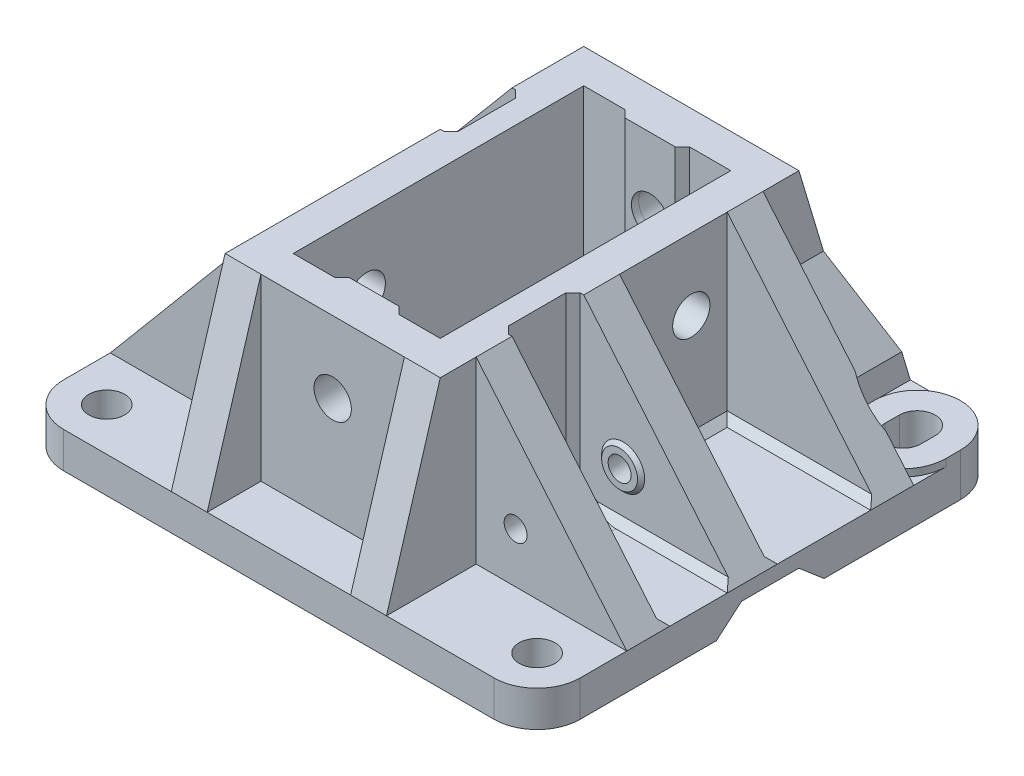
SolidWorks part; units mm, degrees
ref_plane "Front Plane" through (0, 0, 0) normal (0, 0, 1) x (1, 0, 0)
ref_plane "Top Plane" through (0, 0, 0) normal (0, 1, 0) x (1, 0, 0)
ref_plane "Right Plane" through (0, 0, 0) normal (1, 0, 0) x (0, 0, -1)
sketch "Sketch1" plane through (0, 0, 0) normal (0, 1, 0) x (1, 0, 0)
  line L0 (0, 0) -> (0, 65)
  line L1 (0, 0) -> (72, 0)
  line L2 (0, 65) -> (72, 65)
  line L3 (72, 0) -> (72, 65)
  dimension "D1" = 72
  dimension "D2" = 65
extrude "Boss-Extrude1" add sketch "Sketch1" along normal blind 5
sketch "Sketch2" plane through (0, 5, 0) normal (0, 1, 0) x (1, 0, 0)
  line L0 (21, 57.5) -> (21, 7.5)
  line L1 (21, 57.5) -> (51, 57.5)
  line L2 (21, 7.5) -> (51, 7.5)
  line L3 (51, 57.5) -> (51, 7.5)
  line L4 (0, 0) -> (72, 0) construction
  line L7 (72, 0) -> (72, 65) construction
  dimension "D1" = 50
  dimension "D2" = 7.5
  dimension "D3" = 30
  dimension "D4" = 21
extrude "Boss-Extrude2" add sketch "Sketch2" along normal blind 25
sketch "Sketch4" plane through (0, 30, 0) normal (0, 1, 0) x (1, 0, 0)
  line L0 (25.75, 52.75) -> (25.75, 12.25)
  line L1 (25.75, 52.75) -> (46.25, 52.75)
  line L2 (25.75, 12.25) -> (46.25, 12.25)
  line L3 (46.25, 52.75) -> (46.25, 12.25)
  line L4 (51, 57.5) -> (21, 57.5) construction
  line L6 (21, 57.5) -> (21, 7.5) construction
  dimension "D1" = 40.5
  dimension "D2" = 4.75
  dimension "D3" = 20.5
  dimension "D4" = 4.75
extrude "Cut-Extrude1" cut sketch "Sketch4" against normal blind 25
sketch "Sketch5" plane through (51, 0, 0) normal (1, 0, 0) x (0, 0, -1)
  line L0 (57.5, 30) -> (65, 5)
  line L1 (57.5, 5) -> (65, 5)
  line L2 (57.5, 5) -> (57.5, 30)
extrude "Boss-Extrude3" add sketch "Sketch5" against normal blind 5
ref_plane "Plane1" through (36, 0, 0) normal (1, 0, 0) x (0, 0, -1)
mirror "Mirror1" about plane through (36, 0, 0) normal (1, 0, 0) of "Boss-Extrude3"
ref_plane "Plane2" through (0, 0, -32.5) normal (0, 0, 1) x (1, 0, 0)
mirror "Mirror2" about plane through (0, 0, -32.5) normal (0, 0, 1) of "Mirror1", "Boss-Extrude3"
sketch "Sketch6" plane through (0, 0, -7.5) normal (0, 0, 1) x (1, 0, 0)
  line L0 (51, 30) -> (72, 5)
  line L1 (72, 5) -> (51, 5)
  line L2 (51, 5) -> (51, 30)
extrude "Boss-Extrude4" add sketch "Sketch6" against normal blind 5 from offset 5 offset against normal yes
mirror "Mirror3" about plane through (0, 0, -32.5) normal (0, 0, 1) of "Boss-Extrude4"
sketch "Sketch7" plane through (0, 0, -32.5) normal (0, 0, 1) x (1, 0, 0)
  line L0 (51, 30) -> (72, 5)
  line L1 (72, 5) -> (51, 5)
  line L2 (51, 5) -> (51, 30)
extrude "Boss-Extrude5" add sketch "Sketch7" along normal blind 5
mirror "Mirror4" about plane through (36, 0, 0) normal (1, 0, 0) of "Boss-Extrude4", "Mirror3"
sketch "Sketch8" plane through (0, 0, -32.5) normal (0, 0, 1) x (1, 0, 0)
  line L0 (21, 30) -> (0, 5)
  line L1 (0, 5) -> (21, 5)
  line L2 (21, 5) -> (21, 30)
extrude "Boss-Extrude6" add sketch "Sketch8" against normal blind 5
fillet "Fillet1" radius 6 4 edges at (0, 2.5, -65) (0, 2.5, 0) (72, 2.5, 0) (72, 2.5, -65)
sketch "Sketch9" plane through (0, 5, 0) normal (0, 1, 0) x (1, 0, 0)
  line L0 (63.5, 59) -> (63.5, 57)
  line L1 (68.5, 57) -> (68.5, 59)
  line L2 (60, 59) -> (60, 57)
  line L3 (72, 59) -> (72, 57)
  arc A1 (72, 59) -> (60, 59) centre (66, 59) ccw
  arc A2 (63.5, 57) -> (68.5, 57) centre (66, 57) ccw
  arc A3 (68.5, 59) -> (63.5, 59) centre (66, 59) ccw
  arc A4 (72, 59) -> (66, 65) centre (66, 59) ccw construction
  arc A6 (60, 57) -> (72, 57) centre (66, 57) ccw
  point P1 (68.5, 58)
  point P3 (72, 58)
  point P4 (66, 61.5)
  dimension "D1" = 12
  dimension "D2" = 12
  dimension "D3" = 5
  dimension "D4" = 5
  dimension "D5" = 2
  dimension "D6" = 2
  dimension "D7" = 2
  dimension "D8" = 3.5
  dimension "D9" = 3.5
sketch "Sketch10" plane through (72, 0, 0) normal (1, 0, 0) x (0, 0, -1)
  line L0 (36.5, 3) -> (32.5, 3)
  line L1 (0, 0) -> (65, 0) construction
  line L2 (32.5, 5) -> (47.5, 5) construction
  line L3 (36.5, 3) -> (40, 0)
  line L5 (32.5, 5) -> (32.5, 30) construction
  line L6 (28.5, 3) -> (25, 0)
  line L7 (28.5, 3) -> (32.5, 3)
  line L8 (25, 0) -> (40, 0)
  line M7 (6, 0) -> (59, 0)
  dimension "D1" = 4
  dimension "D2" = 25
  dimension "D3" = 3.5
  dimension "D4" = 2
extrude "Cut-Extrude3" cut sketch "Sketch10" against normal blind 75 contours L7 L6 L3 L0 M7
sketch "Sketch11" plane through (0, 5, 0) normal (0, 1, 0) x (1, 0, 0)
  line L0 (51, 0) -> (66, 0) construction
  line L1 (72, 0) -> (72, 65) construction
  circle A0 centre (66, 6) radius 2.5
  dimension "D1" = 5
  dimension "D2" = 6
  dimension "D3" = 6
extrude "Cut-Extrude4" cut sketch "Sketch11" against normal blind 5
mirror "Mirror6" about plane through (36, 0, 0) normal (1, 0, 0) of "Cut-Extrude4"
sketch "Sketch12" plane through (0, 0, -12.5) normal (0, 0, 1) x (1, 0, 0)
  line L0 (51, 30) -> (51, 5) construction
  line L1 (51, 5) -> (72, 5) construction
  circle A0 centre (56.5, 12) radius 1.6
  dimension "D1" = 3.2
  dimension "D2" = 5.5
  dimension "D3" = 7
extrude "Cut-Extrude5" cut sketch "Sketch12" against normal blind 5
sketch "Sketch13" plane through (0, 0, -7.5) normal (0, 0, 1) x (1, 0, 0)
  line L0 (26, 30) -> (46, 30) construction
  line L1 (46, 5) -> (46, 30) construction
  circle A0 centre (36, 20) radius 2.6021
  dimension "D1" = 5.2043
  dimension "D2" = 10
  dimension "D3" = 10
extrude "Cut-Extrude6" cut sketch "Sketch13" against normal blind 7
sketch "Sketch14" plane through (0, 0, -12.25) normal (0, 0, -1) x (-1, 0, 0)
  line L0 (-32.5, 30) -> (-32.5, 5)
  line L1 (-32.5, 30) -> (-39.5, 30)
  line L2 (-32.5, 5) -> (-39.5, 5)
  line L3 (-39.5, 30) -> (-39.5, 5)
  line L4 (-25.75, 30) -> (-46.25, 30) construction
  line L5 (-25.75, 5) -> (-46.25, 5) construction
  dimension "D1" = 7
  dimension "D2" = 6.75
extrude "Boss-Extrude7" add sketch "Sketch14" along normal blind 1
sketch "Sketch15" plane through (0, 30, 0) normal (0, 1, 0) x (1, 0, 0)
  line L0 (39.5, 13.25) -> (40.5, 12.25)
  line L1 (39.5, 12.25) -> (46.25, 12.25) construction
  line L2 (40.5, 12.25) -> (39.5, 12.25)
  line L3 (39.5, 12.25) -> (39.5, 13.25)
  dimension "D1" = 1
extrude "Boss-Extrude8" add sketch "Sketch15" against normal blind 25
mirror "Mirror7" about plane through (36, 0, 0) normal (1, 0, 0) of "Boss-Extrude8"
mirror "Mirror8" about plane through (0, 0, -32.5) normal (0, 0, 1) of "Cut-Extrude6", "Boss-Extrude7", "Mirror7", "Boss-Extrude8"
sketch "Sketch16" plane through (0, 0, -12.25) normal (0, 0, 1) x (1, 0, 0)
  circle A0 centre (36, 20) radius 2.6
  dimension "D1" = 5.2
extrude "Cut-Extrude7" cut sketch "Sketch16" against normal blind 65
ref_plane "Plane3" through (72, 5, -52.5) normal (0, 0, -1) x (-1, 0, 0)
sketch "Sketch21" plane through (0, 30, 0) normal (0, 1, 0) x (1, 0, 0)
  line L0 (21.5, 47.5) -> (22.5, 46.5)
  line L1 (22.5, 46.5) -> (22.5, 38.5)
  line L2 (21, 47.5) -> (21.5, 47.5)
  line L3 (21, 47.5) -> (21, 37.5) construction
  line L4 (21, 47.5) -> (21, 37.5)
  line L5 (21.5, 37.5) -> (22.5, 38.5)
  line L6 (21, 37.5) -> (21.5, 37.5)
  point P9 (21, 42.5)
  dimension "D2" = 0.5
  dimension "D3" = 135
extrude "Cut-Extrude8" cut sketch "Sketch21" against normal blind 25 and the other way through all
fillet "Fillet5" radius 7 3 edges at (22, 5, -38) (22.5, 5, -42.5) (22, 5, -47)
sketch "Sketch22" plane through (0, 30, 0) normal (0, 1, 0) x (1, 0, 0)
  line L0 (51, 17.5) -> (50.4994, 17.5)
  line L1 (50.4994, 17.5) -> (49.4994, 18.5)
  line L2 (49.4994, 18.5) -> (49.4994, 26.5)
  line L5 (51, 27.5) -> (50.4994, 27.5)
  line L6 (50.4994, 27.5) -> (49.4994, 26.5)
  line L7 (51, 17.5) -> (51, 27.5)
  dimension "D1" = 0.5006
  dimension "D2" = 1
  dimension "D3" = 135
extrude "Cut-Extrude9" cut sketch "Sketch22" against normal blind 25
fillet "Fillet6" radius 7 3 edges at (49.9994, 5, -18) (49.4994, 5, -22.5) (49.9994, 5, -27)
sketch "Sketch23" plane through (72, 0, 0) normal (1, 0, 0) x (0, 0, -1)
  line L0 (17.5, 5) -> (17.5, 5.9984)
  line L1 (17.5, 5) -> (18.5023, 5)
  line L2 (17.5, 5) -> (27.5, 5) construction
  line L3 (18.5023, 5) -> (17.5, 5.9984)
extrude "Boss-Extrude10" add sketch "Sketch23" against normal blind 25
sketch "Sketch24" plane through (72, 0, 0) normal (1, 0, 0) x (0, 0, -1)
  line L0 (27.5, 5) -> (27.5, 6)
  line L1 (27.5, 6) -> (26.5, 5)
  line L2 (18.5023, 5) -> (27.5, 5) construction
  line L3 (26.5, 5) -> (27.5, 5)
  dimension "D1" = 1
  dimension "D2" = 1
extrude "Boss-Extrude11" add sketch "Sketch24" against normal blind 25
sketch "Sketch25" plane through (0, 0, -32.5) normal (0, 0, -1) x (-1, 0, 0)
  line L0 (-51, 5) -> (-51, 5.9978)
  line L1 (-51, 30) -> (-51, 5) construction
  line L2 (-51, 5.9978) -> (-52, 5)
  line L3 (-51, 5) -> (-72, 5) construction
  line L4 (-52, 5) -> (-51, 5)
  dimension "D1" = 1
extrude "Boss-Extrude12" add sketch "Sketch25" along normal blind 15
sketch "Sketch26" plane through (72, 0, 0) normal (1, 0, 0) x (0, 0, -1)
  line L0 (32.5, 5) -> (32.5, 5.9972)
  line L1 (32.5, 5.9972) -> (33.5, 5)
  line L2 (32.5, 5) -> (47.5, 5) construction
  line L3 (33.5, 5) -> (32.5, 5)
  dimension "D1" = 1
extrude "Boss-Extrude13" add sketch "Sketch26" against normal blind 25
sketch "Sketch27" plane through (72, 0, 0) normal (1, 0, 0) x (0, 0, -1)
  line L0 (47.5, 5) -> (47.5, 6)
  line L1 (47.5, 6) -> (46.5, 5)
  line L2 (33.5, 5) -> (47.5, 5) construction
  line L3 (46.5, 5) -> (47.5, 5)
  dimension "D1" = 1
  dimension "D2" = 1
extrude "Boss-Extrude14" add sketch "Sketch27" against normal blind 25
ref_plane "Plane4" through (44.6764, 37.5281, 0) normal (0.7657, 0.6432, 0) x (0, 0, -1)
sketch "Sketch28" plane through (44.6764, 37.5281, 0) normal (0.7657, 0.6432, 0) x (0, 0, -1)
  line L0 (11.4122, -43.5785) -> (50.5755, -43.5785)
  line L1 (11.4122, -43.5785) -> (11.4122, -35.2711)
  line L2 (50.5755, -43.5785) -> (50.5755, -35.2711)
  line L3 (11.4122, -35.2711) -> (50.5755, -35.2711)
extrude "Cut-Extrude10" cut sketch "Sketch28" along normal blind 5
sketch "Sketch29" plane through (0, 0, 0) normal (-1, 0, 0) x (0, 0, 1)
  line L0 (-47.5, 5) -> (-47.5, 6)
  line L1 (-47.5, 6) -> (-46.5, 5)
  line L2 (-47.5, 5) -> (-37.5, 5) construction
  line L3 (-46.5, 5) -> (-47.5, 5)
  line L4 (-37.5, 5) -> (-37.5, 6)
  line L5 (-37.5, 6) -> (-38.5, 5)
  line L6 (-38.5, 5) -> (-37.5, 5)
  dimension "D1" = 1
  dimension "D2" = 1
  dimension "D3" = 1
  dimension "D4" = 1
extrude "Boss-Extrude15" add sketch "Sketch29" against normal blind 25
sketch "Sketch30" plane through (0, 0, -32.5) normal (0, 0, 1) x (1, 0, 0)
  line L0 (21, 5) -> (20, 5)
  line L1 (0, 5) -> (21, 5) construction
  line L2 (20, 5) -> (21, 6)
  line L3 (21, 5) -> (21, 30) construction
  line L4 (21, 6) -> (21, 5)
  dimension "D1" = 1
  dimension "D2" = 1
extrude "Boss-Extrude16" add sketch "Sketch30" along normal blind 15
sketch "Sketch31" plane through (0, 0, 0) normal (-1, 0, 0) x (0, 0, 1)
  line L0 (-32.5, 5) -> (-32.5, 6)
  line L1 (-32.5, 6) -> (-31.5, 5)
  line L2 (-32.5, 5) -> (-17.5, 5) construction
  line L3 (-31.5, 5) -> (-32.5, 5)
  line L4 (-17.5, 5) -> (-17.5, 6.0006)
  line L5 (-17.5, 6.0006) -> (-18.5006, 5)
  line L6 (-18.5006, 5) -> (-17.5, 5)
  dimension "D1" = 1.0006
  dimension "D2" = 1.0006
  dimension "D3" = 1
  dimension "D4" = 1
extrude "Boss-Extrude17" add sketch "Sketch31" against normal blind 25
mirror "Mirror10" about plane through (36, 0, 0) normal (1, 0, 0) of "Cut-Extrude10"
sketch "Sketch32" plane through (0, 0, -17.5) normal (0, 0, -1) x (-1, 0, 0)
  circle A0 centre (-56.5, 12) radius 3
  dimension "D1" = 6
extrude "Boss-Extrude18" add sketch "Sketch32" along normal blind 0.5 draft 45
sketch "Sketch33" plane through (0, 0, -12.5) normal (0, 0, 1) x (1, 0, 0)
  circle A0 centre (56.5, 12) radius 1.6
extrude "Cut-Extrude11" cut sketch "Sketch33" against normal blind 20.5
sketch "Sketch34" plane through (0, 0, -27.5) normal (0, 0, 1) x (1, 0, 0)
  circle A0 centre (56.5, 12) radius 3
  dimension "D1" = 6
extrude "Boss-Extrude19" add sketch "Sketch34" along normal blind 0.5 draft 45
sketch "Sketch35" plane through (0, 0, -32.5) normal (0, 0, -1) x (-1, 0, 0)
  circle A0 centre (-56.5, 12) radius 1.6
extrude "Cut-Extrude12" cut sketch "Sketch35" against normal blind 10.5
sketch "Sketch36" plane through (0, 0, -52.5) normal (0, 0, -1) x (-1, 0, 0)
  line L0 (-21, 30) -> (-21, 5) construction
  line L1 (-21, 5) -> (0, 5) construction
  circle A0 centre (-15.5, 12) radius 1.6
  dimension "D1" = 3.2
  dimension "D2" = 5.5
  dimension "D3" = 7
sketch "Sketch37" plane through (0, 0, -47.5) normal (0, 0, 1) x (1, 0, 0)
  circle A0 centre (15.5, 12) radius 3
  dimension "D1" = 6
extrude "Boss-Extrude20" add sketch "Sketch37" along normal blind 0.5 draft 45
sketch "Sketch38" plane through (0, 0, -37.5) normal (0, 0, -1) x (-1, 0, 0)
  circle A0 centre (-15.5, 12) radius 3
  dimension "D1" = 6
extrude "Boss-Extrude21" add sketch "Sketch38" along normal blind 0.5 draft 45
extrude "Cut-Extrude13" cut sketch "Sketch36" against normal blind 20.5
sketch "Sketch40" plane through (21, 0, 0) normal (-1, 0, 0) x (0, 0, 1)
  line L1 (-32.5, 30) -> (-17.5, 30) construction
  line L2 (-17.5, 30) -> (-17.5, 6.0006) construction
  circle A0 centre (-22.5, 20) radius 2.6
  dimension "D1" = 5.2
  dimension "D3" = 5
  dimension "D2" = 10
extrude "Cut-Extrude14" cut sketch "Sketch40" against normal blind 10
sketch "Sketch41" plane through (51, 0, 0) normal (1, 0, 0) x (0, 0, -1)
  line L0 (32.5, 30) -> (47.5, 30) construction
  line L1 (47.5, 30) -> (47.5, 6) construction
  circle A0 centre (42.5, 20) radius 2.6
  point P4 (40, 30)
  dimension "D1" = 5.2
  dimension "D2" = 10
  dimension "D3" = 5
extrude "Cut-Extrude15" cut sketch "Sketch41" against normal blind 10
extrude "Boss-Extrude22" add sketch "Sketch9" along normal blind 1
sketch "Sketch42" plane through (0, 6, 0) normal (0, 1, 0) x (1, 0, 0)
  line L0 (66, 65) -> (72, 65)
  line L1 (72, 65) -> (59.4165, 65)
  arc A0 (72, 59) -> (60, 59) centre (66, 59) ccw construction
ref_plane "Plane5" through (0, 0.8221, 0.0654) normal (0, 0.9968, 0.0793) x (-1, 0, 0)
sketch "Sketch45" plane through (0, 6, 0) normal (0, 1, 0) x (1, 0, 0)
  line L0 (68.1794, 52.5) -> (63.8076, 52.5063)
  line L1 (62.0314, 52.5) -> (69.9686, 52.5) construction
  arc A0 (63.8076, 52.5063) -> (68.1794, 52.5) centre (66, 57) ccw
  dimension "D1" = 10
extrude "Cut-Extrude17" cut sketch "Sketch45" along normal blind 11
sketch "Sketch47" plane through (0, 5, 0) normal (0, 1, 0) x (1, 0, 0)
  line L0 (68.5, 59) -> (68.5, 57)
  line L1 (63.5, 57) -> (63.5, 59)
  arc A0 (63.5, 57) -> (68.5, 57) centre (66, 57) ccw
  arc A1 (68.5, 59) -> (63.5, 59) centre (66, 59) ccw
extrude "Cut-Extrude18" cut sketch "Sketch47" against normal blind 10
mirror "Mirror12" about plane through (36, 0, 0) normal (1, 0, 0) of "Cut-Extrude17", "Boss-Extrude22"
sketch "Sketch48" plane through (0, 0, -52.5) normal (0, 0, -1) x (-1, 0, 0)
  line L0 (-59.0348, 5) -> (-59.0348, 9)
  line L2 (-59.0348, 9) -> (-51, 18.5756)
  line L4 (-51, 5) -> (-62.0314, 5) construction
  line L5 (-51, 5) -> (-59.0348, 5)
  line L12 (-51, 18.5756) -> (-51, 5)
  dimension "D1" = 140
  dimension "D2" = 4
  dimension "D3" = 12.5
extrude "Boss-Extrude23" add sketch "Sketch48" along normal blind 12.5
ref_plane "Plane6" through (0, 18.3028, -61.0092) normal (0, 0.2873, -0.9578) x (-1, 0, 0)
sketch "Sketch49" plane through (0, 18.3028, -61.0092) normal (0, 0.2873, -0.9578) x (-1, 0, 0)
  line L0 (-61.8582, -14.6362) -> (-61.8582, 7.6102)
  line L1 (-61.8582, -14.6362) -> (-48.4009, -14.6362)
  line L2 (-61.8582, 7.6102) -> (-48.4009, 7.6102)
  line L3 (-48.4009, -14.6362) -> (-48.4009, 7.6102)
sketch "Sketch50" plane through (0, 0, -65) normal (0, 0, -1) x (-1, 0, 0)
  line L0 (-59.0348, 9) -> (-59.0348, 5) construction
  line L1 (-66, 5) -> (-59.0348, 5) construction
  circle A0 centre (-52.5348, 7) radius 2
  point P4 (-59.0348, 7)
  dimension "D1" = 4
  dimension "D2" = 6.5
extrude "Cut-Extrude20" cut sketch "Sketch50" against normal blind 12.5
extrude "Cut-Extrude21" cut sketch "Sketch49" along normal blind 12.5
mirror "Mirror13" about plane through (36, 0, 0) normal (1, 0, 0) of "Boss-Extrude22"
sketch "Sketch51" plane through (0, 5, 0) normal (0, 1, 0) x (1, 0, 0)
  line L0 (8.5, 59) -> (8.5, 57)
  line L1 (3.5, 59) -> (3.5, 57)
  arc A0 (3.5, 57) -> (8.5, 57) centre (6, 57) ccw
  arc A1 (8.5, 59) -> (3.5, 59) centre (6, 59) ccw
extrude "Cut-Extrude22" cut sketch "Sketch51" against normal blind 10
